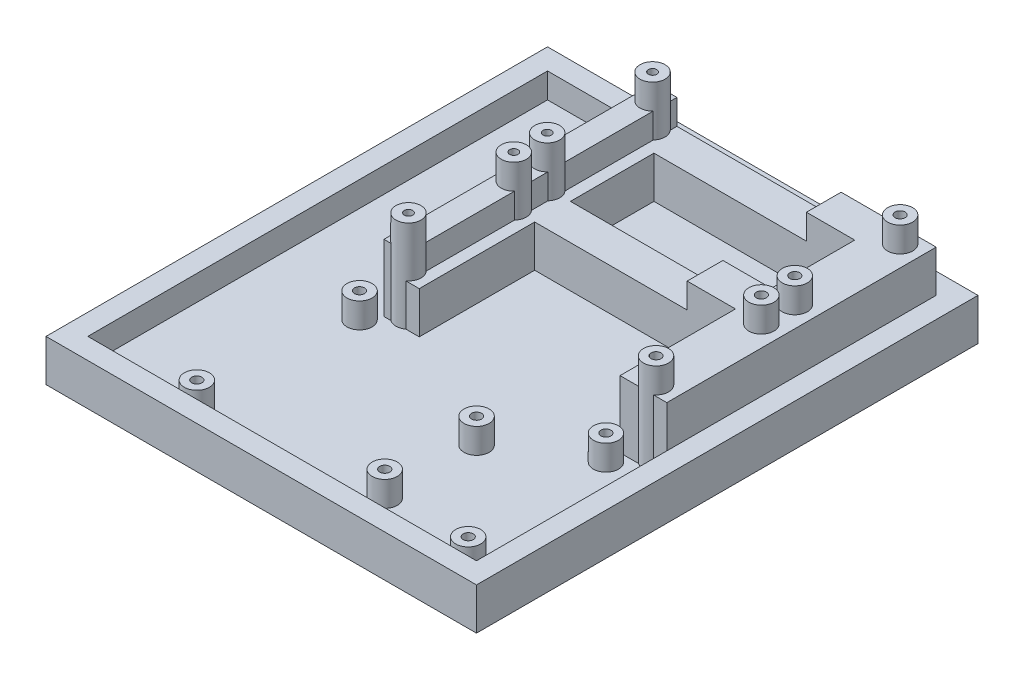
SolidWorks part; units mm, degrees
ref_plane "Front Plane" through (0, 0, 0) normal (0, 0, 1) x (1, 0, 0)
ref_plane "Top Plane" through (0, 0, 0) normal (0, 1, 0) x (1, 0, 0)
ref_plane "Right Plane" through (0, 0, 0) normal (1, 0, 0) x (0, 0, -1)
sketch "Sketch1" plane through (0, 0, 0) normal (0, 1, 0) x (1, 0, 0)
  line L1 (-76.2, -76.2) -> (76.2, -76.2)
  line L2 (-76.2, -76.2) -> (-76.2, 76.2)
  line L3 (-76.2, 76.2) -> (76.2, 76.2)
  line L4 (76.2, -76.2) -> (76.2, 76.2)
  line L5 (-76.2, -76.2) -> (76.2, 76.2) construction
  line L6 (-76.2, 76.2) -> (76.2, -76.2) construction
  point P0 (0, 0)
  dimension "D1" = 152.4
  dimension "D2" = 152.4
extrude "Boss-Extrude1" add sketch "Sketch1" along normal blind 5.08
sketch "Sketch6" plane through (0, 5.08, 0) normal (0, 1, 0) x (1, 0, 0)
  line L0 (76.2, -76.2) -> (76.2, 76.2) construction
  line L2 (-76.2, -76.2) -> (76.2, -76.2) construction
  line L3 (67.31, 76.2) -> (67.31, -76.2) construction
  line L4 (76.2, 76.2) -> (-76.2, 76.2) construction
  line L5 (-76.2, -67.31) -> (76.2, -67.31) construction
  line L6 (-76.2, 76.2) -> (-76.2, -76.2) construction
  circle A0 centre (62.2605, -64.77) radius 3.81
  circle A1 centre (-20.2108, -64.77) radius 3.81
  circle A2 centre (31.811, -59.69) radius 3.81
  circle A3 centre (31.811, -31.7805) radius 3.81
  circle A4 centre (55.9003, -16.5506) radius 3.81
  circle A5 centre (-18.9789, -16.5506) radius 3.81
  dimension "D1" = 7.62
  dimension "D5" = 7.62
  dimension "D7" = 7.62
  dimension "D13" = 7.62
  dimension "D16" = 7.62
  dimension "D19" = 7.62
  dimension "D2" = 5.0495
  dimension "D3" = 2.54
  dimension "D4" = 82.4713
  dimension "D6" = 35.499
  dimension "D8" = 8.89
  dimension "D9" = 8.89
  dimension "D10" = 2.54
  dimension "D11" = 7.62
  dimension "D12" = 35.499
  dimension "D14" = 35.5295
  dimension "D15" = 11.4097
  dimension "D17" = 50.7594
  dimension "D18" = 86.2889
extrude "Boss-Extrude3" add sketch "Sketch6" along normal blind 7.62
sketch "Sketch7" plane through (0, 5.08, 0) normal (0, 1, 0) x (1, 0, 0)
  line L0 (-69.85, 69.85) -> (-69.85, -69.85)
  line L1 (-76.2, 76.2) -> (76.2, 76.2)
  line L2 (-76.2, 76.2) -> (-76.2, -76.2)
  line L3 (-76.2, -76.2) -> (76.2, -76.2)
  line L4 (76.2, 76.2) -> (76.2, -76.2)
  line L5 (-69.85, -69.85) -> (69.85, -69.85)
  line L6 (69.85, 69.85) -> (69.85, -69.85)
  line L7 (-69.85, 69.85) -> (69.85, 69.85)
  dimension "D1" = 6.35
extrude "Boss-Extrude4" add sketch "Sketch7" along normal blind 7.62
sketch "Sketch9" plane through (0, 5.08, 0) normal (0, 1, 0) x (1, 0, 0)
  line L0 (69.85, -69.85) -> (69.85, 69.85) construction
  line L2 (-36.2484, 7.0714) -> (96.5902, 7.0714) construction
  line L3 (-59.5162, 28.1534) -> (104.81, 28.1534) construction
  circle A0 centre (63.5, -8.9306) radius 3.81
  circle A1 centre (55.9003, -16.5506) radius 3.81 construction
  circle A2 centre (-11.7348, -8.9306) radius 3.81
  circle A3 centre (63.5, 23.0734) radius 3.81
  circle A4 centre (-11.7348, 23.0734) radius 3.81
  circle A5 centre (-11.7348, 33.2334) radius 3.81
  circle A6 centre (63.5, 33.2334) radius 3.81
  circle A7 centre (63.5, 65.2374) radius 3.81
  circle A8 centre (-11.7348, 65.2374) radius 3.81
  point P8 (55.9003, -16.5506)
  dimension "D1" = 6.35
  dimension "D2" = 7.62
  dimension "D4" = 7.62
  dimension "D3" = 7.62
  dimension "D5" = 75.2348
  dimension "D6" = 16.002
  dimension "D7" = 5.08
extrude "Boss-Extrude6" add sketch "Sketch9" along normal blind 27.94
sketch "Sketch11" plane through (0, 5.08, 0) normal (0, 1, 0) x (1, 0, 0)
  line L1 (69.85, 69.85) -> (-16.1137, 69.85)
  line L2 (69.85, 69.85) -> (69.85, -12.0015)
  line L3 (69.85, -12.0015) -> (-16.1137, -12.0015)
  line L4 (-16.1137, 69.85) -> (-16.1137, -12.0015)
extrude "Boss-Extrude9" add sketch "Sketch11" along normal blind 20.32
sketch "Sketch12" plane through (0, 25.4, 0) normal (0, 1, 0) x (1, 0, 0)
  line L0 (69.85, 69.85) -> (-16.1137, 69.85) construction
  line L1 (-5.3848, 69.85) -> (55.6297, 69.85)
  line L2 (-5.3848, 69.85) -> (-5.3848, -12.0015)
  line L3 (-5.3848, -12.0015) -> (55.6297, -12.0015)
  line L4 (55.6297, 69.85) -> (55.6297, -12.0015)
  line L5 (-9.4796, -12.0015) -> (61.2448, -12.0015) construction
  line L6 (-5.3848, 59.3148) -> (55.6297, 59.3148)
  line L7 (-5.3848, 33.9295) -> (55.6297, 33.9295)
  line L8 (55.6297, 23.0734) -> (-5.3848, 23.0734)
  point P15 (-11.7348, 65.2374)
  dimension "D1" = 6.35
extrude "Cut-Extrude1" cut sketch "Sketch12" against normal blind 20.32
sketch "Sketch14" plane through (0, 25.4, 0) normal (0, 1, 0) x (1, 0, 0)
  line L0 (69.85, 69.85) -> (-16.1137, 69.85) construction
  line L1 (-5.3848, 69.85) -> (40.9509, 69.85)
  line L2 (-5.3848, 69.85) -> (-5.3848, 23.0734)
  line L3 (-5.3848, 23.0734) -> (40.9509, 23.0734)
  line L4 (40.9509, 69.85) -> (40.9509, 23.0734)
  line L5 (55.6297, 23.0734) -> (-5.3848, 23.0734) construction
extrude "Cut-Extrude2" cut sketch "Sketch14" against normal blind 7.62
sketch "Sketch15" plane through (0, 12.7, 0) normal (0, 1, 0) x (1, 0, 0)
  circle A0 centre (-18.9789, -16.5506) radius 1.524
  circle A1 centre (31.811, -31.7805) radius 1.524
  circle A2 centre (55.9003, -16.5506) radius 1.524
  circle A3 centre (62.2605, -64.77) radius 1.524
  circle A4 centre (31.811, -59.69) radius 1.524
  circle A5 centre (-20.2108, -64.77) radius 1.524
  dimension "D1" = 3.048
  dimension "D2" = 3.048
  dimension "D3" = 3.048
  dimension "D4" = 3.048
  dimension "D5" = 3.048
  dimension "D6" = 3.048
extrude "Cut-Extrude3" cut sketch "Sketch15" against normal blind 3.81
sketch "Sketch16" plane through (0, 33.02, 0) normal (0, 1, 0) x (1, 0, 0)
  line L0 (25.8826, 65.2374) -> (25.8826, -8.9306) construction
  circle A0 centre (63.5, 65.2374) radius 1.524
  circle A1 centre (63.5, 33.2334) radius 1.524
  circle A2 centre (63.5, 23.0734) radius 1.524
  circle A3 centre (63.5, -8.9306) radius 1.524
  circle A4 centre (-11.7348, -8.9306) radius 1.524
  circle A5 centre (-11.7348, 23.0734) radius 1.524
  circle A6 centre (-11.7348, 33.2334) radius 1.524
  circle A7 centre (-11.7348, 65.2374) radius 1.524
  dimension "D1" = 3.048
  dimension "D2" = 3.048
  dimension "D3" = 3.048
  dimension "D4" = 3.048
extrude "Cut-Extrude4" cut sketch "Sketch16" against normal blind 3.81
sketch "Sketch18" plane through (0, 0, 0) normal (0, -1, 0) x (1, 0, 0)
  line L1 (82.55, -82.55) -> (-82.55, -82.55)
  line L2 (82.55, -82.55) -> (82.55, 82.55)
  line L3 (82.55, 82.55) -> (-82.55, 82.55)
  line L4 (-82.55, -82.55) -> (-82.55, 82.55)
  line L5 (82.55, -82.55) -> (-82.55, 82.55) construction
  line L6 (82.55, 82.55) -> (-82.55, -82.55) construction
  line L7 (76.2, 76.2) -> (-76.2, 76.2)
  line L8 (76.2, 76.2) -> (76.2, -76.2)
  line L9 (76.2, -76.2) -> (-76.2, -76.2)
  line L10 (-76.2, 76.2) -> (-76.2, -76.2)
  line L11 (76.2, 76.2) -> (-76.2, -76.2) construction
  line L12 (76.2, -76.2) -> (-76.2, 76.2) construction
  point P0 (0, 0)
  point P6 (0, 0)
  dimension "D1" = 165.1
extrude "Boss-Extrude10" add sketch "Sketch18" against normal up to vertex
sketch "Sketch22" plane through (0, 12.7, 0) normal (0, 1, 0) x (1, 0, 0)
  line L0 (-69.85, 69.85) -> (-69.85, -69.85) construction
  line L1 (-76.2, 76.2) -> (76.2, 76.2)
  line L2 (-76.2, 76.2) -> (-76.2, -76.2)
  line L3 (-76.2, -76.2) -> (76.2, -76.2)
  line L4 (76.2, 76.2) -> (76.2, -76.2)
  line L5 (-82.55, 82.55) -> (82.55, 82.55) construction
  line L6 (82.55, 82.55) -> (82.55, -82.55) construction
  line L7 (82.55, -82.55) -> (-82.55, -82.55) construction
  line L9 (-101.3646, 97.3248) -> (94.2071, 97.3248)
  line L10 (-101.3646, 97.3248) -> (-101.3646, -102.6583)
  line L11 (-101.3646, -102.6583) -> (94.2071, -102.6583)
  line L12 (94.2071, 97.3248) -> (94.2071, -102.6583)
  dimension "D1" = 6.35
  dimension "D2" = 6.35
  dimension "D3" = 6.35
  dimension "D4" = 6.35
extrude "Cut-Extrude5" cut sketch "Sketch22" against normal through all
sketch "Sketch24" plane through (0, 12.7, 0) normal (0, 1, 0) x (1, 0, 0)
  line L0 (-76.2, -76.2) -> (76.2, -76.2) construction
  line L1 (-76.2, 76.2) -> (-54.61, 76.2)
  line L2 (-76.2, 76.2) -> (-76.2, -76.2)
  line L3 (-76.2, -76.2) -> (-54.61, -76.2)
  line L4 (-54.61, 76.2) -> (-54.61, -76.2)
  dimension "D1" = 21.59
extrude "Cut-Extrude6" cut sketch "Sketch24" against normal through all
sketch "Sketch25" plane through (0, 5.08, 0) normal (0, 1, 0) x (1, 0, 0)
  line L0 (-54.61, -69.85) -> (69.85, -69.85) construction
  line L1 (-54.61, 69.85) -> (-48.26, 69.85)
  line L2 (-54.61, 69.85) -> (-54.61, -69.85)
  line L3 (-54.61, -69.85) -> (-48.26, -69.85)
  line L4 (-48.26, 69.85) -> (-48.26, -69.85)
  dimension "D1" = 6.35
extrude "Boss-Extrude11" add sketch "Sketch25" along normal up to surface (7.62 mm away) up to face at (12.7396, 12.7, -5.7849)
sketch "Sketch26" plane through (0, 25.4, 0) normal (0, 1, 0) x (1, 0, 0)
  line L1 (-5.3848, 69.85) -> (-8.9408, 69.85)
  line L2 (-5.3848, 69.85) -> (-5.3848, -12.0015)
  line L3 (-5.3848, -12.0015) -> (-8.9408, -12.0015)
  line L4 (-8.9408, 69.85) -> (-8.9408, -12.0015)
  dimension "D1" = 3.556
extrude "Cut-Extrude7" cut sketch "Sketch26" against normal up to surface (7.62 mm away) up to face at (17.783, 17.78, -64.5824)
sketch "Sketch28" plane through (0, 33.02, 0) normal (0, 1, 0) x (1, 0, 0)
  circle A0 centre (-11.7348, 65.2374) radius 1.27
  circle A1 centre (-11.7348, 65.2374) radius 3.81
  circle A2 centre (-11.7348, 33.2334) radius 1.27
  circle A3 centre (-11.7348, 33.2334) radius 3.81
  circle A4 centre (-11.7348, 23.0734) radius 1.27
  circle A5 centre (-11.7348, 23.0734) radius 3.81
  circle A6 centre (-11.7348, -8.9306) radius 1.27
  circle A7 centre (-11.7348, -8.9306) radius 3.81
extrude "Boss-Extrude12" add sketch "Sketch28" against normal through all
sketch "Sketch29" plane through (0, 33.02, 0) normal (0, 1, 0) x (1, 0, 0)
  line L0 (-8.9408, -11.5209) -> (-8.9408, -12.0015)
  line L1 (-9.4796, -12.0015) -> (-5.3848, -12.0015) construction
  line L2 (-9.4796, -12.0015) -> (-8.9408, -12.0015) construction
  line L3 (-8.9408, -12.0015) -> (-9.4796, -12.0015)
  circle A0 centre (-11.7348, -8.9306) radius 3.81
extrude "Cut-Extrude8" cut sketch "Sketch29" against normal up to surface (15.24 mm away) contours L3 L0 M2 up to face at (3.1622, 17.78, -31.8644)
